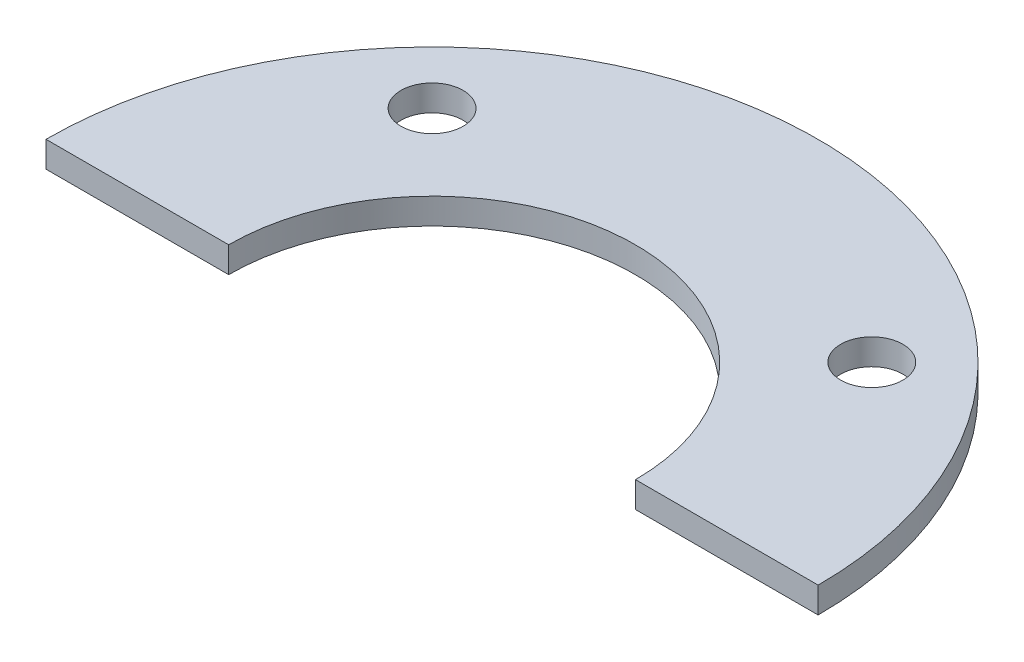
SolidWorks part; units mm, degrees
material "Plain Carbon Steel"
ref_plane "Front Plane" through (0, 0, 0) normal (0, 0, 1) x (1, 0, 0)
ref_plane "Top Plane" through (0, 0, 0) normal (0, 1, 0) x (1, 0, 0)
ref_plane "Right Plane" through (0, 0, 0) normal (1, 0, 0) x (0, 0, -1)
sketch "Sketch1" plane through (0, 0, 0) normal (0, 1, 0) x (1, 0, 0)
  line L0 (-9.9695, 0) -> (-18.923, 0)
  line L1 (9.9695, 0) -> (18.923, 0)
  line L2 (-55, 0) -> (55, 0) construction
  arc A0 (-9.9695, 0) -> (9.9695, 0) centre (0, 0) cw
  arc A1 (-18.923, 0) -> (18.923, 0) centre (0, 0) cw
  dimension "D2" = 18.923
  dimension "D1" = 19.939
extrude "Boss-Extrude1" add sketch "Sketch1" along normal blind 1.27
sketch "Sketch2" plane through (0, 1.27, 0) normal (0, 1, 0) x (1, 0, 0)
  line L0 (-10.7763, 10.7763) -> (0, 0) construction
  line L1 (0, 0) -> (10.7763, 10.7763) construction
  line L2 (0, -0.6985) -> (0, 0.6985) construction
  arc A0 (-10.7763, 10.7763) -> (10.7763, 10.7763) centre (0, 0) cw construction
  circle A1 centre (-10.7763, 10.7763) radius 1.524
  circle A2 centre (10.7763, 10.7763) radius 1.524
  dimension "D4" = 3.048
  dimension "D1" = 45
  dimension "D2" = 45
  dimension "D3" = 15.24
extrude "Cut-Extrude1" cut sketch "Sketch2" against normal through all
